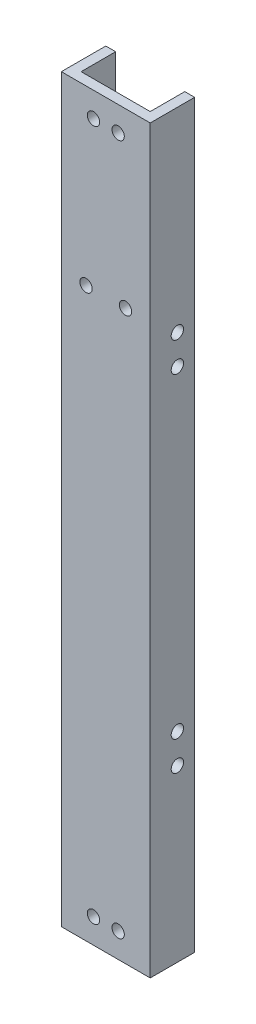
SolidWorks part; units mm, degrees
ref_plane "Front Plane" through (0, 0, 0) normal (0, 0, 1) x (1, 0, 0)
ref_plane "Top Plane" through (0, 0, 0) normal (0, 1, 0) x (1, 0, 0)
ref_plane "Right Plane" through (0, 0, 0) normal (1, 0, 0) x (0, 0, -1)
sketch "Sketch1" plane through (0, 0, 0) normal (0, 1, 0) x (1, 0, 0)
  line L0 (-7, 4.5) -> (-7, -2.5)
  line L2 (-9, 4.5) -> (-9, -4.5)
  line L3 (-9, -4.5) -> (9, -4.5)
  line L4 (9, 4.5) -> (9, -4.5)
  line L5 (-9, 4.5) -> (9, -4.5) construction
  line L6 (-9, -4.5) -> (9, 4.5) construction
  line L7 (-7, -2.5) -> (7, -2.5)
  line L8 (7, 4.5) -> (7, -2.5)
  line L9 (-9, 4.5) -> (-7, 4.5)
  line L10 (9, 4.5) -> (7, 4.5)
  point P0 (0, 0)
  dimension "D1" = 18
  dimension "D2" = 9
  dimension "D4" = 14
  dimension "D5" = 9
  dimension "D3" = 2
extrude "Boss-Extrude1" add sketch "Sketch1" along normal blind 150
sketch "Sketch2" plane through (0, 0, 2.5) normal (0, 0, -1) x (-1, 0, 0)
  line L0 (0, 150) -> (0, 0) construction
  line L1 (-7, 150) -> (7, 150) construction
  line L2 (-7, 2) -> (7, 2) construction
  line L3 (-7, 150) -> (-7, 0) construction
  line L4 (7, 150) -> (7, 0) construction
  line L5 (-7, 0) -> (7, 0) construction
  line L6 (-9, 75) -> (9, 75) construction
  line L7 (-9, 150) -> (-9, 0) construction
  line L8 (9, 150) -> (9, 0) construction
  circle A0 centre (-2.5, 5) radius 1.25
  circle A1 centre (2.5, 5) radius 1.25
  circle A2 centre (2.5, 145) radius 1.25
  circle A3 centre (-2.5, 145) radius 1.25
  dimension "D2" = 2.5
  dimension "D3" = 2.5
  dimension "D1" = 2
  dimension "D4" = 5
  dimension "D5" = 2.5
  dimension "D6" = 3
  dimension "D7" = 3
extrude "Cut-Extrude1" cut sketch "Sketch2" against normal blind 10
sketch "Sketch3" plane through (0, 0, 4.5) normal (0, 0, 1) x (1, 0, 0)
  line L0 (0, 150) -> (0, 0) construction
  line L1 (-9, 150) -> (9, 150) construction
  circle A0 centre (0, 100.9296) radius 3.4035
sketch "Sketch5" plane through (9, 0, 0) normal (1, 0, 0) x (0, 0, -1)
  line L0 (-4.5, 75) -> (4.5, 75) construction
  line L1 (-4.5, 150) -> (-4.5, 0) construction
  line L2 (4.5, 150) -> (4.5, 0) construction
  line L3 (-4.5, 75) -> (4.5, 75) construction
  line L4 (-4.5, 150) -> (-4.5, 0) construction
  line L5 (-4.5, 0) -> (4.5, 0) construction
  line L6 (-4.5, 107.5) -> (4.5, 107.5) construction
  line L7 (-4.5, 37.5) -> (4.5, 37.5) construction
  line L9 (-1.9353, 114) -> (4.5, 114) construction
  line L10 (-1.9353, 114) -> (-1.9353, 100.1444) construction
  line L11 (-1.9353, 100.1444) -> (4.5, 100.1444) construction
  line L12 (4.5, 114) -> (4.5, 100.1444) construction
  circle A0 centre (1, 110.5) radius 1.25
  circle A1 centre (1, 104.5) radius 1.25
  circle A4 centre (1, 40.5) radius 1.25
  circle A5 centre (1, 34.5) radius 1.25
  dimension "D6" = 2.5
  dimension "D7" = 2.5
  dimension "D3" = 2.5
  dimension "D13" = 2.5
  dimension "D1" = 75
  dimension "D2" = 70
  dimension "D4" = 6
  dimension "D5" = 3
  dimension "D8" = 3.5
  dimension "D9" = 3.5
  dimension "D10" = 3.5
  dimension "D11" = 4.3556
  dimension "D12" = 2.9353
  dimension "D14" = 3.5
  dimension "D15" = 3.5
  dimension "D16" = 6
  dimension "D17" = 3
extrude "Cut-Extrude2" cut sketch "Sketch5" against normal through all both and the other way through all
sketch "Sketch7" plane through (0, 0, 4.5) normal (0, 0, 1) x (1, 0, 0)
  line L0 (0, 150) -> (0, 0) construction
  line L1 (-9, 150) -> (9, 150) construction
  line L2 (-9, 150) -> (-9, 0) construction
  circle A0 centre (-4, 115) radius 1.25
  circle A1 centre (4, 115) radius 1.25
  dimension "D1" = 2.5
  dimension "D2" = 5
  dimension "D3" = 35
extrude "Cut-Extrude3" cut sketch "Sketch7" against normal up to surface (2 mm away) up to face at (3.75, 145, 2.5)
